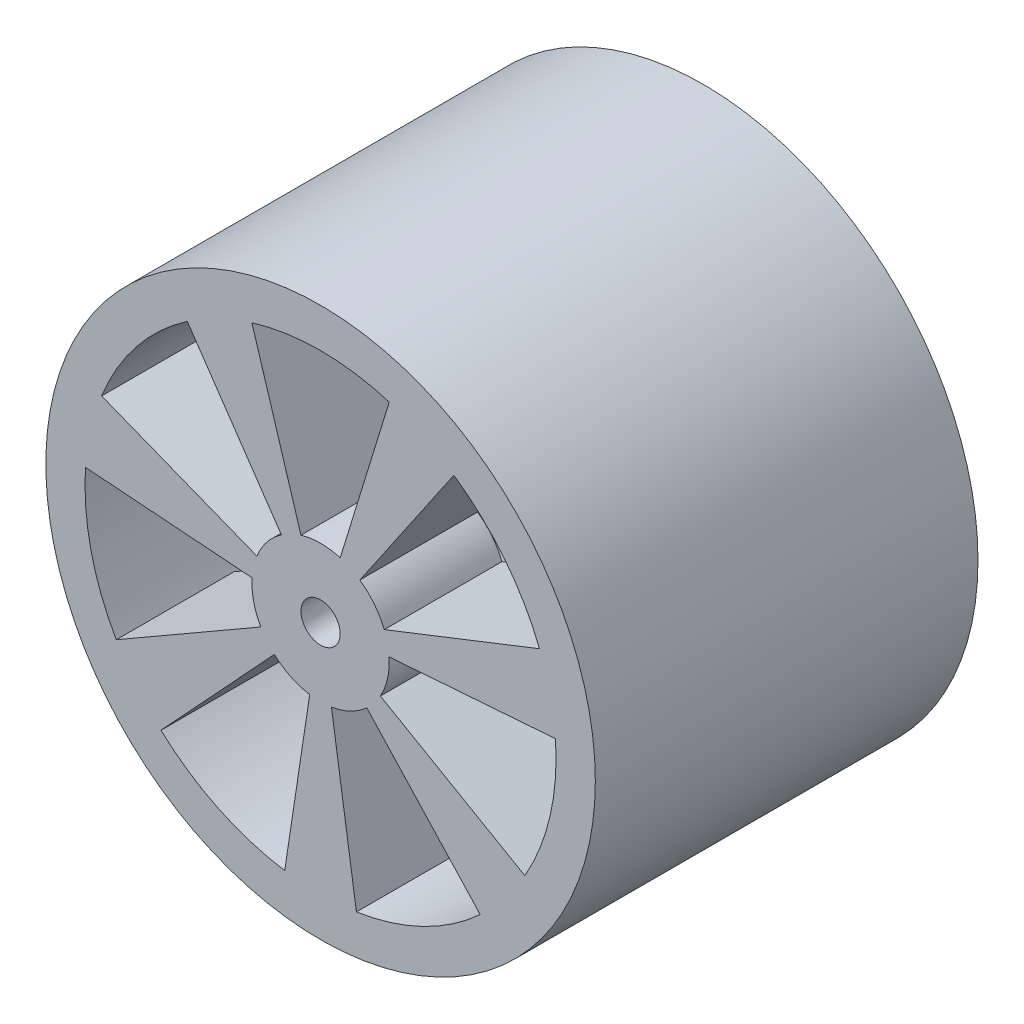
SolidWorks part; units mm, degrees
material "Nylon 101"
ref_plane "Front Plane" through (0, 0, 0) normal (0, 0, 1) x (1, 0, 0)
ref_plane "Top Plane" through (0, 0, 0) normal (0, 1, 0) x (1, 0, 0)
ref_plane "Right Plane" through (0, 0, 0) normal (1, 0, 0) x (0, 0, -1)
sketch "Sketch1" plane through (0, 0, 0) normal (0, 0, 1) x (1, 0, 0)
  circle A0 centre (0, 0) radius 28
  circle A1 centre (0, 0) radius 2
  dimension "D1" = 56
  dimension "D2" = 4
extrude "Boss-Extrude1" add sketch "Sketch1" along normal blind 39
sketch "Sketch2" plane through (0, 0, 0) normal (0, 0, -1) x (-1, 0, 0)
  circle A0 centre (0, 0) radius 24
  dimension "D1" = 48
extrude "Cut-Extrude1" cut sketch "Sketch2" against normal offset from surface (27 mm away) 12 up to face at (28, 0, 39)
sketch "Sketch3" plane through (0, 0, 27) normal (0, 0, -1) x (-1, 0, 0)
  line L1 (6, 0) -> (3, 5.1962)
  line L2 (3, 5.1962) -> (-3, 5.1962)
  line L3 (-3, 5.1962) -> (-6, 0)
  line L4 (-6, 0) -> (-3, -5.1962)
  line L5 (-3, -5.1962) -> (3, -5.1962)
  line L6 (3, -5.1962) -> (6, 0)
  circle A0 centre (0, 0) radius 6 construction
  dimension "D1" = 12
extrude "Cut-Extrude2" cut sketch "Sketch3" against normal blind 4
sketch "Sketch5" plane through (0, 0, 39) normal (0, 0, 1) x (1, 0, 0)
  line L0 (0, 7) -> (0, 24) construction
  line L1 (-7, 22.9565) -> (-2, 6.7082)
  line L2 (2, 6.7082) -> (7, 22.9565)
  line L3 (13.5837, 19.786) -> (3.9977, 5.7462)
  line L4 (6.4917, 2.6188) -> (22.3125, 8.8403)
  line L5 (23.9386, 1.7162) -> (6.9851, 0.4571)
  line L6 (6.095, -3.4426) -> (20.8233, -11.9328)
  line L7 (16.2672, -17.6459) -> (4.7125, -5.1761)
  line L8 (1.1086, -6.9117) -> (3.6537, -23.7203)
  line L9 (-3.6537, -23.7203) -> (-1.1086, -6.9117)
  line L10 (-4.7125, -5.1761) -> (-16.2672, -17.6459)
  line L11 (-20.8233, -11.9328) -> (-6.095, -3.4426)
  line L12 (-6.9851, 0.4571) -> (-23.9386, 1.7162)
  line L13 (-22.3125, 8.8403) -> (-6.4917, 2.6188)
  line L14 (-3.9977, 5.7462) -> (-13.5837, 19.786)
  arc A0 (-3.9977, 5.7462) -> (-6.4917, 2.6188) centre (0, 0) ccw
  arc A1 (-13.5837, 19.786) -> (-22.3125, 8.8403) centre (0, 0) ccw
  arc A2 (-7, 22.9565) -> (7, 22.9565) centre (0, 0) cw
  arc A3 (-2, 6.7082) -> (2, 6.7082) centre (0, 0) cw
  arc A4 (3.9977, 5.7462) -> (6.4917, 2.6188) centre (0, 0) cw
  arc A5 (13.5837, 19.786) -> (22.3125, 8.8403) centre (0, 0) cw
  arc A6 (6.9851, 0.4571) -> (6.095, -3.4426) centre (0, 0) cw
  arc A7 (23.9386, 1.7162) -> (20.8233, -11.9328) centre (0, 0) cw
  arc A8 (4.7125, -5.1761) -> (1.1086, -6.9117) centre (0, 0) cw
  arc A9 (16.2672, -17.6459) -> (3.6537, -23.7203) centre (0, 0) cw
  arc A10 (-1.1086, -6.9117) -> (-4.7125, -5.1761) centre (0, 0) cw
  arc A11 (-3.6537, -23.7203) -> (-16.2672, -17.6459) centre (0, 0) cw
  arc A12 (-6.095, -3.4426) -> (-6.9851, 0.4571) centre (0, 0) cw
  arc A13 (-20.8233, -11.9328) -> (-23.9386, 1.7162) centre (0, 0) cw
  arc A28 (-6.4917, 2.6188) -> (-3.9977, 5.7462) centre (0, 0) cw [skipped]
  arc A29 (-22.3125, 8.8403) -> (-13.5837, 19.786) centre (0, 0) cw [skipped]
  point P36 (0, 0)
  dimension "D1" = 14
  dimension "D2" = 48
  dimension "D5" = 14
  dimension "D3" = 4
  dimension "D4" = 7
extrude "Cut-Extrude4" cut sketch "Sketch5" against normal through all
